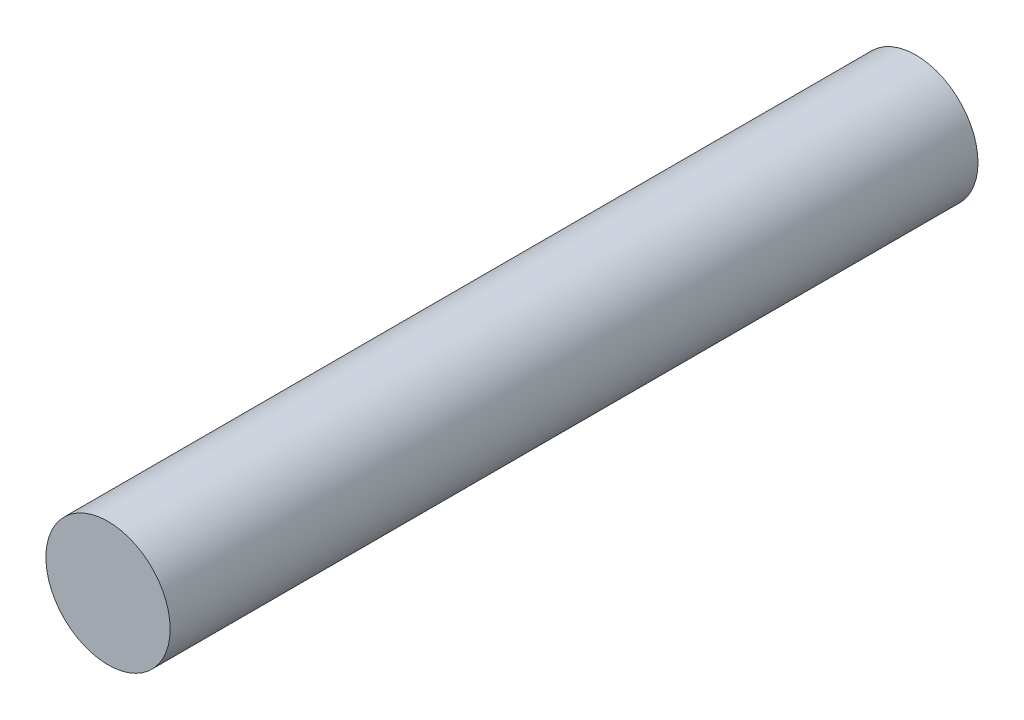
SolidWorks part; units mm, degrees
ref_plane "Front Plane" through (0, 0, 0) normal (0, 0, 1) x (1, 0, 0)
ref_plane "Top Plane" through (0, 0, 0) normal (0, 1, 0) x (1, 0, 0)
ref_plane "Right Plane" through (0, 0, 0) normal (1, 0, 0) x (0, 0, -1)
sketch "Sketch1" plane through (0, 0, 0) normal (0, 0, 1) x (1, 0, 0)
  circle A0 centre (0, 0) radius 5
extrude "Boss-Extrude1" add sketch "Sketch1" along normal blind 65
